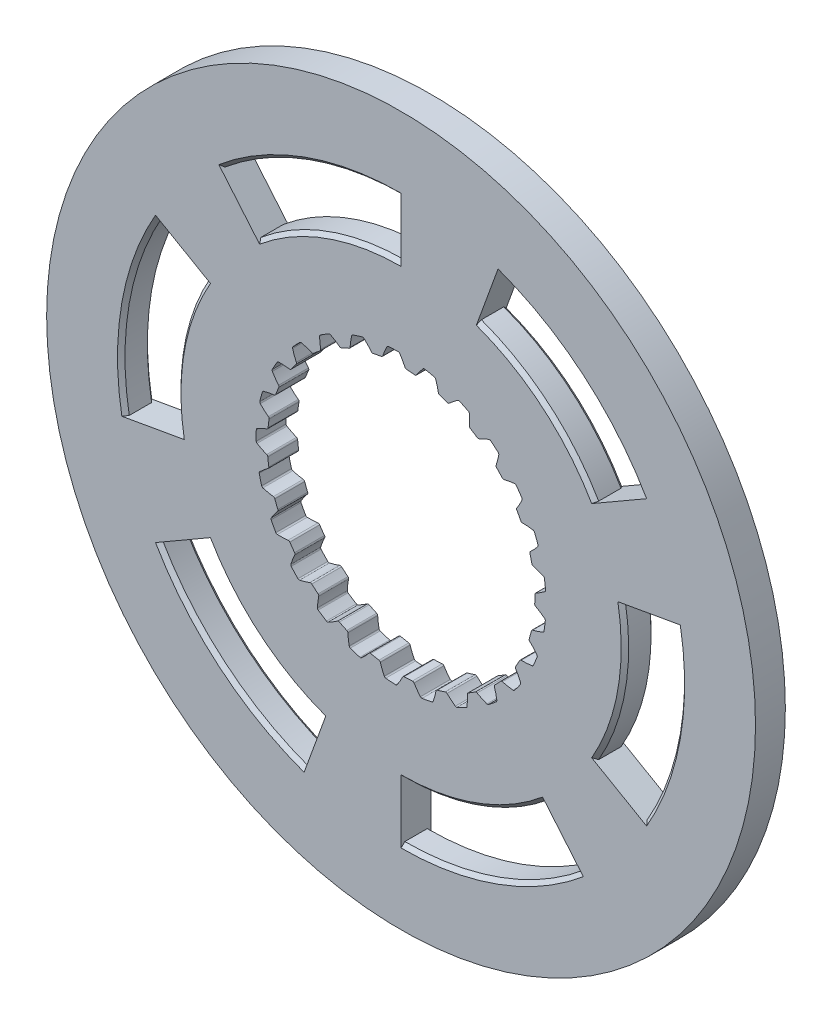
SolidWorks part; units mm, degrees
material "1.6587 (18CrNiMo7-6)"
ref_plane "Front Plane" through (0, 0, 0) normal (0, 0, 1) x (1, 0, 0)
ref_plane "Top Plane" through (0, 0, 0) normal (0, 1, 0) x (1, 0, 0)
ref_plane "Right Plane" through (0, 0, 0) normal (1, 0, 0) x (0, 0, -1)
sketch "Sketch1" plane through (0, 0, 0) normal (0, 0, 1) x (1, 0, 0)
  circle A0 centre (0, 0) radius 35.85
  circle A1 centre (0, 0) radius 95
  dimension "D1" = 71.7
  dimension "D2" = 190
extrude "Boss-Extrude1" add sketch "Sketch1" along normal blind 8
sketch "Sketch2" plane through (0, 0, 8) normal (0, 0, 1) x (1, 0, 0)
  line L0 (0, 0) -> (37.4458, 2.0146) construction
  line L1 (0, 0) -> (45.8703, 5.3719) construction
  circle A0 centre (0, 0) radius 37.5 construction
  arc A1 (35.8337, 1.0823) -> (35.1141, 7.2265) centre (0, 0) ccw
  arc A2 (38.7391, 2.9335) -> (38.3686, 6.0967) centre (0, 0) ccw
  spline S0 degree 4 poles (32.476, 0) (32.4914, 0.0003) (32.5344, 0.0018) (32.6158, 0.0079) (32.7482, 0.0223) (32.9164, 0.0473) (33.1329, 0.0872) (33.3867, 0.1439) (33.6639, 0.2163) (33.9634, 0.3059) (34.2601, 0.4048) (34.554, 0.5124) (34.8448, 0.6274) (35.1945, 0.7761) (35.6099, 0.9672) (36.0896, 1.2091) (36.626, 1.5052) (37.164, 1.8298) (37.6859, 2.1679) (38.2038, 2.5305) (38.6983, 2.8963) (39.2016, 3.2972) (39.6609, 3.6779) (40.1632, 4.1272) (40.5651, 4.4965) (41.0814, 5.0072) (41.3822, 5.3158) (41.7292, 5.685) (41.8807, 5.8532) (41.9741, 5.9566) knots 0 0 0 0 0 0.005377 0.015084 0.028532 0.04661 0.064855 0.092111 0.119476 0.146842 0.174209 0.201575 0.228941 0.256307 0.307035 0.361767 0.4165 0.471232 0.525964 0.580697 0.635429 0.690161 0.744894 0.799626 0.854358 0.909091 0.954545 1 1 1 1 1 construction
  spline S1 degree 4 poles (35.8337, 1.0823) (35.9646, 1.1484) (36.2334, 1.2885) (36.6345, 1.5103) (37.164, 1.8298) (37.6859, 2.1679) (38.1493, 2.4923) (38.4702, 2.7278) (38.667, 2.8779) (38.7391, 2.9335) knots 0.310476 0.310476 0.310476 0.310476 0.310476 0.361767 0.4165 0.471232 0.525964 0.580697 0.612361 0.612361 0.612361 0.612361 0.612361
  spline S2 degree 4 poles (35.1141, 7.2265) (35.2567, 7.1924) (35.5506, 7.1182) (35.9922, 6.9951) (36.5812, 6.8065) (37.167, 6.5982) (37.6928, 6.3896) (38.0595, 6.2347) (38.2857, 6.1342) (38.3686, 6.0967) knots 0.310476 0.310476 0.310476 0.310476 0.310476 0.361767 0.4165 0.471232 0.525964 0.580697 0.612361 0.612361 0.612361 0.612361 0.612361
  dimension "D1" = 75
  dimension "D2" = 71.7
  dimension "D3" = 77.7
  dimension "D4" = 3.6
extrude "Cut-Extrude1" cut sketch "Sketch2" against normal blind 8
fillet "Fillet1" radius 0.48 4 edges at (35.8337, 1.0823, 4) (38.7391, 2.9335, 4) (35.1141, 7.2265, 4) (38.3686, 6.0967, 4)
pattern_circular "CirPattern1" count 25 over 360 about axis through (0, 0, 8) along (0, 0, -1) of "Cut-Extrude1", "Fillet1"
sketch "Sketch3" plane through (0, 0, 8) normal (0, 0, 1) x (1, 0, 0)
  line L0 (0, 0) -> (0, 101.6605)
  line L1 (0, 0) -> (35.4301, 97.3435)
  line L2 (0, 0) -> (102.017, 17.9883)
  line L3 (0, 0) -> (88.0406, 50.8303)
  line L4 (0, 0) -> (66.5869, -79.3551)
  line L5 (0, 0) -> (88.0406, -50.8303)
  line L6 (0, 0) -> (-35.4301, -97.3435)
  line L7 (0, 0) -> (0, -101.6605)
  line L8 (0, 0) -> (-102.017, -17.9883)
  line L9 (0, 0) -> (-88.0406, -50.8303)
  line L10 (0, 0) -> (-66.5869, 79.3551)
  line L11 (0, 0) -> (-88.0406, 50.8303)
  circle A0 centre (0, 0) radius 75
  circle A1 centre (0, 0) radius 60
  point P19 (0, 0)
  dimension "D1" = 150
  dimension "D2" = 120
  dimension "D3" = 20
  dimension "D4" = 6
extrude "Cut-Extrude2" cut sketch "Sketch3" against normal blind 8 contours A1 L0 A0 L10 | A1 L11 A0 L8 | A1 L9 A0 L6 | A1 L3 A0 L1 | A1 L5 A0 L2 | A1 L7 A0 L4
chamfer "Chamfer1" distance 1 24 edges at (59.0885, -10.4189, 8) (73.8606, -13.0236, 8) (-38.5673, -45.9627, 8) (25.6515, -70.4769, 8) (-73.8606, 13.0236, 8) (-48.2091, -57.4533, 8) (-38.5673, -45.9627, 0) (-48.2091, -57.4533, 0) (25.6515, -70.4769, 0) (73.8606, -13.0236, 0) (20.5212, -56.3816, 8) (20.5212, -56.3816, 0) (59.0885, -10.4189, 0) (38.5673, 45.9627, 0) (-25.6515, 70.4769, 0) (-73.8606, 13.0236, 0) (-20.5212, 56.3816, 0) (48.2091, 57.4533, 0) (48.2091, 57.4533, 8) (38.5673, 45.9627, 8) (-59.0885, 10.4189, 0) (-59.0885, 10.4189, 8) (-25.6515, 70.4769, 8) (-20.5212, 56.3816, 8)
